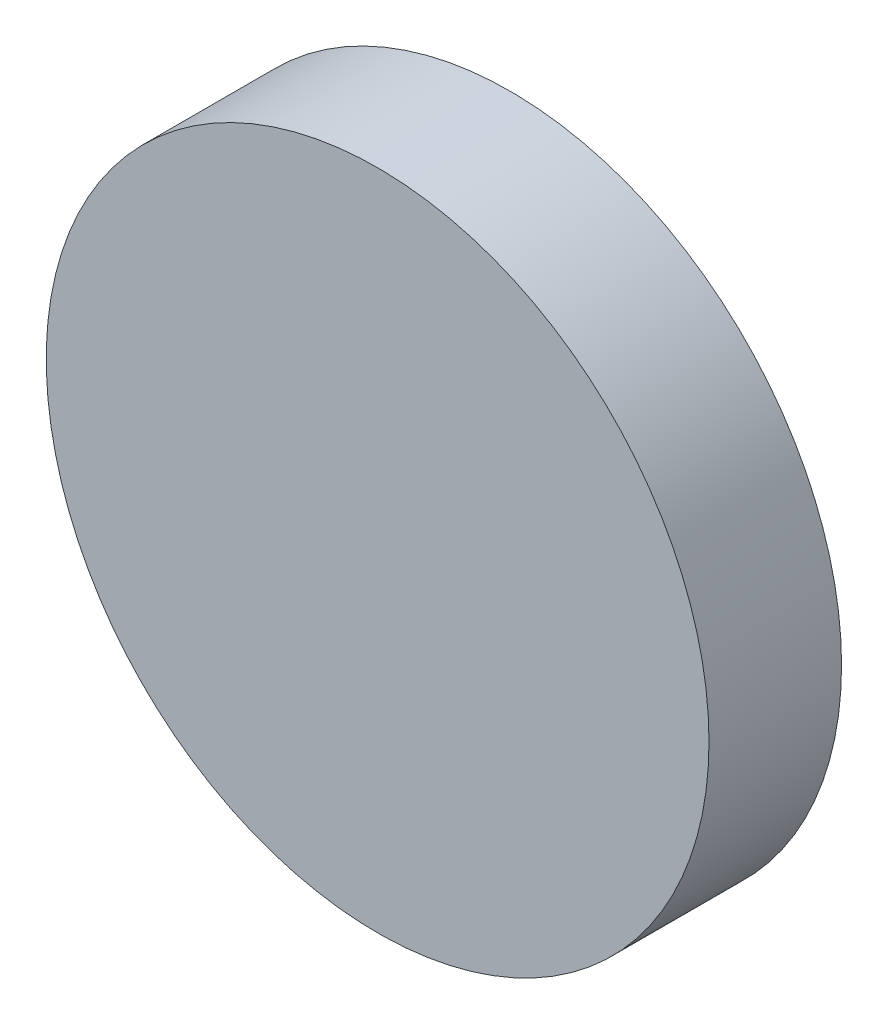
SolidWorks part; units mm, degrees
ref_plane "前视基准面" through (0, 0, 0) normal (0, 0, 1) x (1, 0, 0)
ref_plane "上视基准面" through (0, 0, 0) normal (0, 1, 0) x (1, 0, 0)
ref_plane "右视基准面" through (0, 0, 0) normal (1, 0, 0) x (0, 0, -1)
sketch "草图1" plane through (0, 0, 0) normal (0, 0, 1) x (1, 0, 0)
  circle A0 centre (0, 0) radius 10
  dimension "D1" = 20
extrude "凸台-拉伸1" add sketch "草图1" along normal blind 4 contours A0
